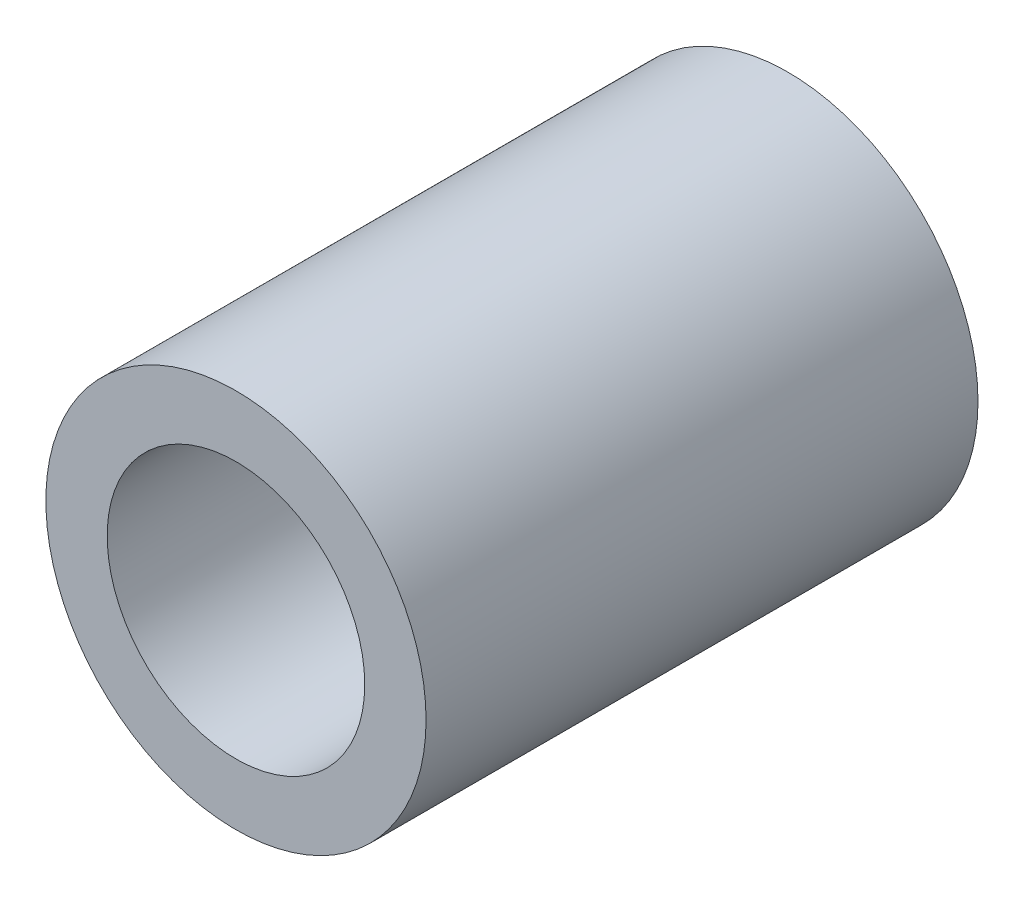
SolidWorks part; units mm, degrees
ref_plane "Front Plane" through (0, 0, 0) normal (0, 0, 1) x (1, 0, 0)
ref_plane "Top Plane" through (0, 0, 0) normal (0, 1, 0) x (1, 0, 0)
ref_plane "Right Plane" through (0, 0, 0) normal (1, 0, 0) x (0, 0, -1)
sketch "Sketch1" plane through (0, 0, 0) normal (0, 0, 1) x (1, 0, 0)
  circle A0 centre (0, 0) radius 2.1
  circle A1 centre (0, 0) radius 3.1
  dimension "D1" = 6.2
  dimension "D2" = 4.2
extrude "Boss-Extrude1" add sketch "Sketch1" along normal blind 9
equation "\"height\"= 9mm"
equation "\"height 2\"= 3mm"
equation "\"D1@Boss-Extrude1\" = \"height\""
